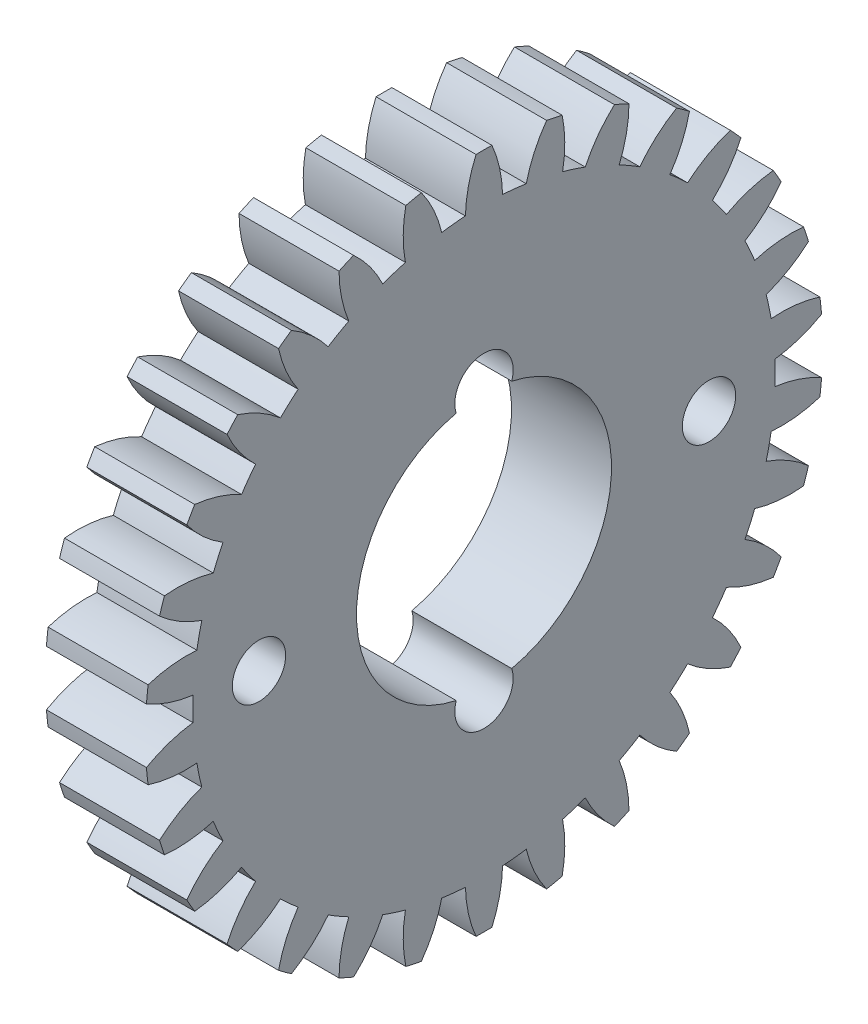
SolidWorks part; units mm, degrees
material "Aço 4140"
ref_plane "Plano frontal" through (0, 0, 0) normal (0, 0, 1) x (1, 0, 0)
ref_plane "Plano superior" through (0, 0, 0) normal (0, 1, 0) x (1, 0, 0)
ref_plane "Plano direito" through (0, 0, 0) normal (1, 0, 0) x (0, 0, -1)
ref_plane "Plano1" through (0, 0, 0) normal (-1, 0, 0) x (0, -1, 0)
sketch "Esboço1" plane through (0, 0, 0) normal (-1, 0, 0) x (0, -1, 0)
  circle A0 centre (8, 0) radius 1.75
  circle A1 centre (0, 0) radius 3
  circle A2 centre (-8, 0) radius 1.75
  arc A3 (17.4396, -1.1143) -> (20.3144, -0.4769) centre (17.2585, 6.5035) ccw
  arc A4 (20.3144, -0.4769) -> (20.3144, 0.4769) centre (0, 0) ccw
  arc A5 (20.3144, 0.4769) -> (17.4396, 1.1143) centre (17.2585, -6.5035) ccw
  arc A6 (17.4396, 1.1143) -> (17.2902, 2.5359) centre (0, 0) ccw
  arc A7 (17.2902, 2.5359) -> (19.9696, 3.7571) centre (15.5292, 9.9496) ccw
  arc A8 (19.9696, 3.7571) -> (19.7713, 4.6901) centre (0, 0) ccw
  arc A9 (19.7713, 4.6901) -> (16.8269, 4.7159) centre (18.2335, -2.7732) ccw
  arc A10 (16.8269, 4.7159) -> (16.3851, 6.0754) centre (0, 0) ccw
  arc A11 (16.3851, 6.0754) -> (18.7521, 7.827) centre (13.1212, 12.9609) ccw
  arc A12 (18.7521, 7.827) -> (18.3642, 8.6983) centre (0, 0) ccw
  arc A13 (18.3642, 8.6983) -> (15.4787, 8.1113) centre (18.4117, 1.0784) ccw
  arc A14 (15.4787, 8.1113) -> (14.7639, 9.3493) centre (0, 0) ccw
  arc A15 (14.7639, 9.3493) -> (16.715, 11.5547) centre (10.1398, 15.4058) ccw
  arc A16 (16.715, 11.5547) -> (16.1544, 12.3263) centre (0, 0) ccw
  arc A17 (16.1544, 12.3263) -> (13.454, 11.1523) centre (17.7851, 4.8828) ccw
  arc A18 (13.454, 11.1523) -> (12.4975, 12.2145) centre (0, 0) ccw
  arc A19 (12.4975, 12.2145) -> (13.9474, 14.7775) centre (6.7151, 17.1773) ccw
  arc A20 (13.9474, 14.7775) -> (13.2386, 15.4156) centre (0, 0) ccw
  arc A21 (13.2386, 15.4156) -> (10.8413, 13.7058) centre (16.3813, 8.4739) ccw
  arc A22 (10.8413, 13.7058) -> (9.6849, 14.546) centre (0, 0) ccw
  arc A23 (9.6849, 14.546) -> (10.5702, 17.3544) centre (2.997, 18.1981) ccw
  arc A24 (10.5702, 17.3544) -> (9.7442, 17.8312) centre (0, 0) ccw
  arc A25 (9.7442, 17.8312) -> (7.7548, 15.6603) centre (14.2615, 11.6946) ccw
  arc A26 (7.7548, 15.6603) -> (6.4489, 16.2417) centre (0, 0) ccw
  arc A27 (6.4489, 16.2417) -> (6.731, 19.1728) centre (-0.852, 18.4235) ccw
  arc A28 (6.731, 19.1728) -> (5.824, 19.4675) centre (0, 0) ccw
  arc A29 (5.824, 19.4675) -> (4.3294, 16.9304) centre (11.5184, 14.4041) ccw
  arc A30 (4.3294, 16.9304) -> (2.9312, 17.2276) centre (0, 0) ccw
  arc A31 (2.9312, 17.2276) -> (2.5977, 20.1533) centre (-4.6639, 17.8438) ccw
  arc A32 (2.5977, 20.1533) -> (1.6492, 20.253) centre (0, 0) ccw
  arc A33 (1.6492, 20.253) -> (0.7147, 17.4606) centre (8.2719, 16.4842) ccw
  arc A34 (0.7147, 17.4606) -> (-0.7147, 17.4606) centre (0, 0) ccw
  arc A35 (-0.7147, 17.4606) -> (-1.6492, 20.253) centre (-8.2719, 16.4842) ccw
  arc A36 (-1.6492, 20.253) -> (-2.5977, 20.1533) centre (0, 0) ccw
  arc A37 (-2.5977, 20.1533) -> (-2.9312, 17.2276) centre (4.6639, 17.8438) ccw
  arc A38 (-2.9312, 17.2276) -> (-4.3294, 16.9304) centre (0, 0) ccw
  arc A39 (-4.3294, 16.9304) -> (-5.824, 19.4675) centre (-11.5184, 14.4041) ccw
  arc A40 (-5.824, 19.4675) -> (-6.731, 19.1728) centre (0, 0) ccw
  arc A41 (-6.731, 19.1728) -> (-6.4489, 16.2417) centre (0.852, 18.4235) ccw
  arc A42 (-6.4489, 16.2417) -> (-7.7548, 15.6603) centre (0, 0) ccw
  arc A43 (-7.7548, 15.6603) -> (-9.7442, 17.8312) centre (-14.2615, 11.6946) ccw
  arc A44 (-9.7442, 17.8312) -> (-10.5702, 17.3544) centre (0, 0) ccw
  arc A45 (-10.5702, 17.3544) -> (-9.6849, 14.546) centre (-2.997, 18.1981) ccw
  arc A46 (-9.6849, 14.546) -> (-10.8413, 13.7058) centre (0, 0) ccw
  arc A47 (-10.8413, 13.7058) -> (-13.2386, 15.4156) centre (-16.3813, 8.4739) ccw
  arc A48 (-13.2386, 15.4156) -> (-13.9474, 14.7775) centre (0, 0) ccw
  arc A49 (-13.9474, 14.7775) -> (-12.4975, 12.2145) centre (-6.7151, 17.1773) ccw
  arc A50 (-12.4975, 12.2145) -> (-13.454, 11.1523) centre (0, 0) ccw
  arc A51 (-13.454, 11.1523) -> (-16.1544, 12.3263) centre (-17.7851, 4.8828) ccw
  arc A52 (-16.1544, 12.3263) -> (-16.715, 11.5547) centre (0, 0) ccw
  arc A53 (-16.715, 11.5547) -> (-14.7639, 9.3493) centre (-10.1398, 15.4058) ccw
  arc A54 (-14.7639, 9.3493) -> (-15.4787, 8.1113) centre (0, 0) ccw
  arc A55 (-15.4787, 8.1113) -> (-18.3642, 8.6983) centre (-18.4117, 1.0784) ccw
  arc A56 (-18.3642, 8.6983) -> (-18.7521, 7.827) centre (0, 0) ccw
  arc A57 (-18.7521, 7.827) -> (-16.3851, 6.0754) centre (-13.1212, 12.9609) ccw
  arc A58 (-16.3851, 6.0754) -> (-16.8269, 4.7159) centre (0, 0) ccw
  arc A59 (-16.8269, 4.7159) -> (-19.7713, 4.6901) centre (-18.2335, -2.7732) ccw
  arc A60 (-19.7713, 4.6901) -> (-19.9696, 3.7571) centre (0, 0) ccw
  arc A61 (-19.9696, 3.7571) -> (-17.2902, 2.5359) centre (-15.5292, 9.9496) ccw
  arc A62 (-17.2902, 2.5359) -> (-17.4396, 1.1143) centre (0, 0) ccw
  arc A63 (-17.4396, 1.1143) -> (-20.3144, 0.4769) centre (-17.2585, -6.5035) ccw
  arc A64 (-20.3144, 0.4769) -> (-20.3144, -0.4769) centre (0, 0) ccw
  arc A65 (-20.3144, -0.4769) -> (-17.4396, -1.1143) centre (-17.2585, 6.5035) ccw
  arc A66 (-17.4396, -1.1143) -> (-17.2902, -2.5359) centre (0, 0) ccw
  arc A67 (-17.2902, -2.5359) -> (-19.9696, -3.7571) centre (-15.5292, -9.9496) ccw
  arc A68 (-19.9696, -3.7571) -> (-19.7713, -4.6901) centre (0, 0) ccw
  arc A69 (-19.7713, -4.6901) -> (-16.8269, -4.7159) centre (-18.2335, 2.7732) ccw
  arc A70 (-16.8269, -4.7159) -> (-16.3851, -6.0754) centre (0, 0) ccw
  arc A71 (-16.3851, -6.0754) -> (-18.7521, -7.827) centre (-13.1212, -12.9609) ccw
  arc A72 (-18.7521, -7.827) -> (-18.3642, -8.6983) centre (0, 0) ccw
  arc A73 (-18.3642, -8.6983) -> (-15.4787, -8.1113) centre (-18.4117, -1.0784) ccw
  arc A74 (-15.4787, -8.1113) -> (-14.7639, -9.3493) centre (0, 0) ccw
  arc A75 (-14.7639, -9.3493) -> (-16.715, -11.5547) centre (-10.1398, -15.4058) ccw
  arc A76 (-16.715, -11.5547) -> (-16.1544, -12.3263) centre (0, 0) ccw
  arc A77 (-16.1544, -12.3263) -> (-13.454, -11.1523) centre (-17.7851, -4.8828) ccw
  arc A78 (-13.454, -11.1523) -> (-12.4975, -12.2145) centre (0, 0) ccw
  arc A79 (-12.4975, -12.2145) -> (-13.9474, -14.7775) centre (-6.7151, -17.1773) ccw
  arc A80 (-13.9474, -14.7775) -> (-13.2386, -15.4156) centre (0, 0) ccw
  arc A81 (-13.2386, -15.4156) -> (-10.8413, -13.7058) centre (-16.3813, -8.4739) ccw
  arc A82 (-10.8413, -13.7058) -> (-9.6849, -14.546) centre (0, 0) ccw
  arc A83 (-9.6849, -14.546) -> (-10.5702, -17.3544) centre (-2.997, -18.1981) ccw
  arc A84 (-10.5702, -17.3544) -> (-9.7442, -17.8312) centre (0, 0) ccw
  arc A85 (-9.7442, -17.8312) -> (-7.7548, -15.6603) centre (-14.2615, -11.6946) ccw
  arc A86 (-7.7548, -15.6603) -> (-6.4489, -16.2417) centre (0, 0) ccw
  arc A87 (-6.4489, -16.2417) -> (-6.731, -19.1728) centre (0.852, -18.4235) ccw
  arc A88 (-6.731, -19.1728) -> (-5.824, -19.4675) centre (0, 0) ccw
  arc A89 (-5.824, -19.4675) -> (-4.3294, -16.9304) centre (-11.5184, -14.4041) ccw
  arc A90 (-4.3294, -16.9304) -> (-2.9312, -17.2276) centre (0, 0) ccw
  arc A91 (-2.9312, -17.2276) -> (-2.5977, -20.1533) centre (4.6639, -17.8438) ccw
  arc A92 (-2.5977, -20.1533) -> (-1.6492, -20.253) centre (0, 0) ccw
  arc A93 (-1.6492, -20.253) -> (-0.7147, -17.4606) centre (-8.2719, -16.4842) ccw
  arc A94 (-0.7147, -17.4606) -> (0.7147, -17.4606) centre (0, 0) ccw
  arc A95 (0.7147, -17.4606) -> (1.6492, -20.253) centre (8.2719, -16.4842) ccw
  arc A96 (1.6492, -20.253) -> (2.5977, -20.1533) centre (0, 0) ccw
  arc A97 (2.5977, -20.1533) -> (2.9312, -17.2276) centre (-4.6639, -17.8438) ccw
  arc A98 (2.9312, -17.2276) -> (4.3294, -16.9304) centre (0, 0) ccw
  arc A99 (4.3294, -16.9304) -> (5.824, -19.4675) centre (11.5184, -14.4041) ccw
  arc A100 (5.824, -19.4675) -> (6.731, -19.1728) centre (0, 0) ccw
  arc A101 (6.731, -19.1728) -> (6.4489, -16.2417) centre (-0.852, -18.4235) ccw
  arc A102 (6.4489, -16.2417) -> (7.7548, -15.6603) centre (0, 0) ccw
  arc A103 (7.7548, -15.6603) -> (9.7442, -17.8312) centre (14.2615, -11.6946) ccw
  arc A104 (9.7442, -17.8312) -> (10.5702, -17.3544) centre (0, 0) ccw
  arc A105 (10.5702, -17.3544) -> (9.6849, -14.546) centre (2.997, -18.1981) ccw
  arc A106 (9.6849, -14.546) -> (10.8413, -13.7058) centre (0, 0) ccw
  arc A107 (10.8413, -13.7058) -> (13.2386, -15.4156) centre (16.3813, -8.4739) ccw
  arc A108 (13.2386, -15.4156) -> (13.9474, -14.7775) centre (0, 0) ccw
  arc A109 (13.9474, -14.7775) -> (12.4975, -12.2145) centre (6.7151, -17.1773) ccw
  arc A110 (12.4975, -12.2145) -> (13.454, -11.1523) centre (0, 0) ccw
  arc A111 (13.454, -11.1523) -> (16.1544, -12.3263) centre (17.7851, -4.8828) ccw
  arc A112 (16.1544, -12.3263) -> (16.715, -11.5547) centre (0, 0) ccw
  arc A113 (16.715, -11.5547) -> (14.7639, -9.3493) centre (10.1398, -15.4058) ccw
  arc A114 (14.7639, -9.3493) -> (15.4787, -8.1113) centre (0, 0) ccw
  arc A115 (15.4787, -8.1113) -> (18.3642, -8.6983) centre (18.4117, -1.0784) ccw
  arc A116 (18.3642, -8.6983) -> (18.7521, -7.827) centre (0, 0) ccw
  arc A117 (18.7521, -7.827) -> (16.3851, -6.0754) centre (13.1212, -12.9609) ccw
  arc A118 (16.3851, -6.0754) -> (16.8269, -4.7159) centre (0, 0) ccw
  arc A119 (16.8269, -4.7159) -> (19.7713, -4.6901) centre (18.2335, 2.7732) ccw
  arc A120 (19.7713, -4.6901) -> (19.9696, -3.7571) centre (0, 0) ccw
  arc A121 (19.9696, -3.7571) -> (17.2902, -2.5359) centre (15.5292, -9.9496) ccw
  arc A122 (17.2902, -2.5359) -> (17.4396, -1.1143) centre (0, 0) ccw
extrude "Ressalto-extrusão1" add sketch "Esboço1" against normal blind 6
sketch "Esboço2" plane through (6, 0, 0) normal (1, 0, 0) x (0, 0, -1)
  line L0 (-13.5, 0) -> (13.5, 0) construction
  circle A0 centre (-13.5, 0) radius 1.6
  circle A1 centre (13.5, 0) radius 1.6
  circle A2 centre (0, 0) radius 7.65
  dimension "D1" = 15.3
  dimension "D2" = 3.2
  dimension "D3" = 27
extrude "Corte-extrusão1" cut sketch "Esboço2" against normal through all both
sketch "Esboço3" plane through (0, 0, 0) normal (1, 0, 0) x (0, 0, -1)
  circle A0 centre (13.5, 0) radius 3.25
  circle A1 centre (-13.5, 0) radius 3.25
  dimension "D1" = 6.5
extrude "Corte-extrusão3" cut sketch "Esboço3" along normal blind 3
